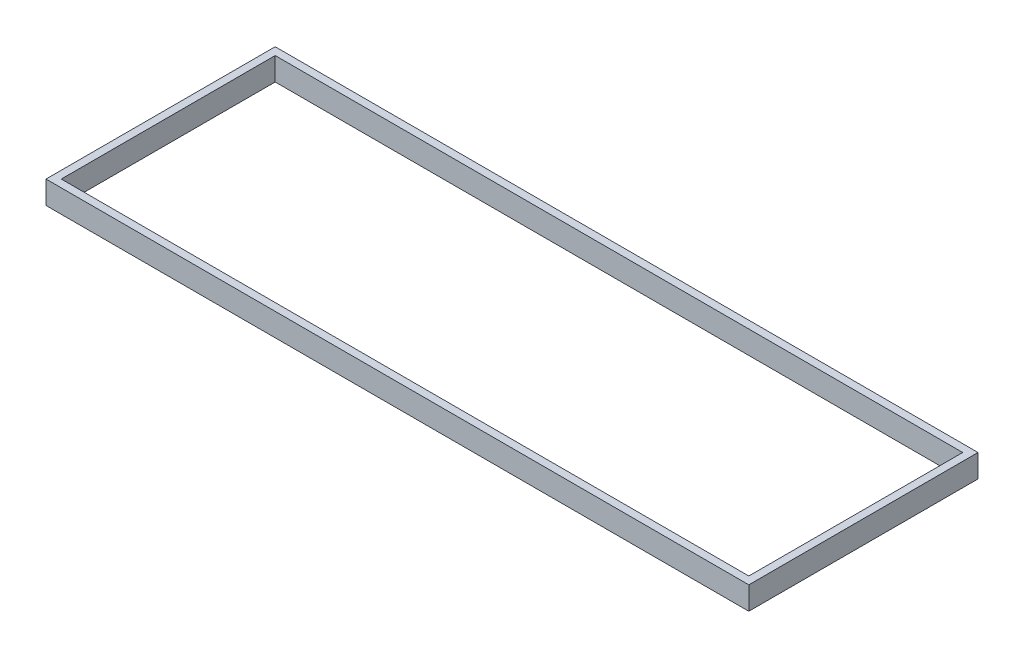
SolidWorks part; units mm, degrees
ref_plane "Front Plane" through (0, 0, 0) normal (0, 0, 1) x (1, 0, 0)
ref_plane "Top Plane" through (0, 0, 0) normal (0, 1, 0) x (1, 0, 0)
ref_plane "Right Plane" through (0, 0, 0) normal (1, 0, 0) x (0, 0, -1)
sketch "Sketch1" plane through (0, 0, 0) normal (0, 1, 0) x (1, 0, 0)
  line L1 (-45, 14) -> (45, 14)
  line L2 (-45, 14) -> (-45, -14)
  line L3 (-45, -14) -> (45, -14)
  line L4 (45, 14) -> (45, -14)
  line L5 (-45, 14) -> (45, -14) construction
  line L6 (-45, -14) -> (45, 14) construction
  point P0 (0, 0)
  dimension "D1" = 90
  dimension "D2" = 28
extrude "Extrude-Thin1" add sketch "Sketch1" along normal blind 3 thin thin type one direction wall 1
